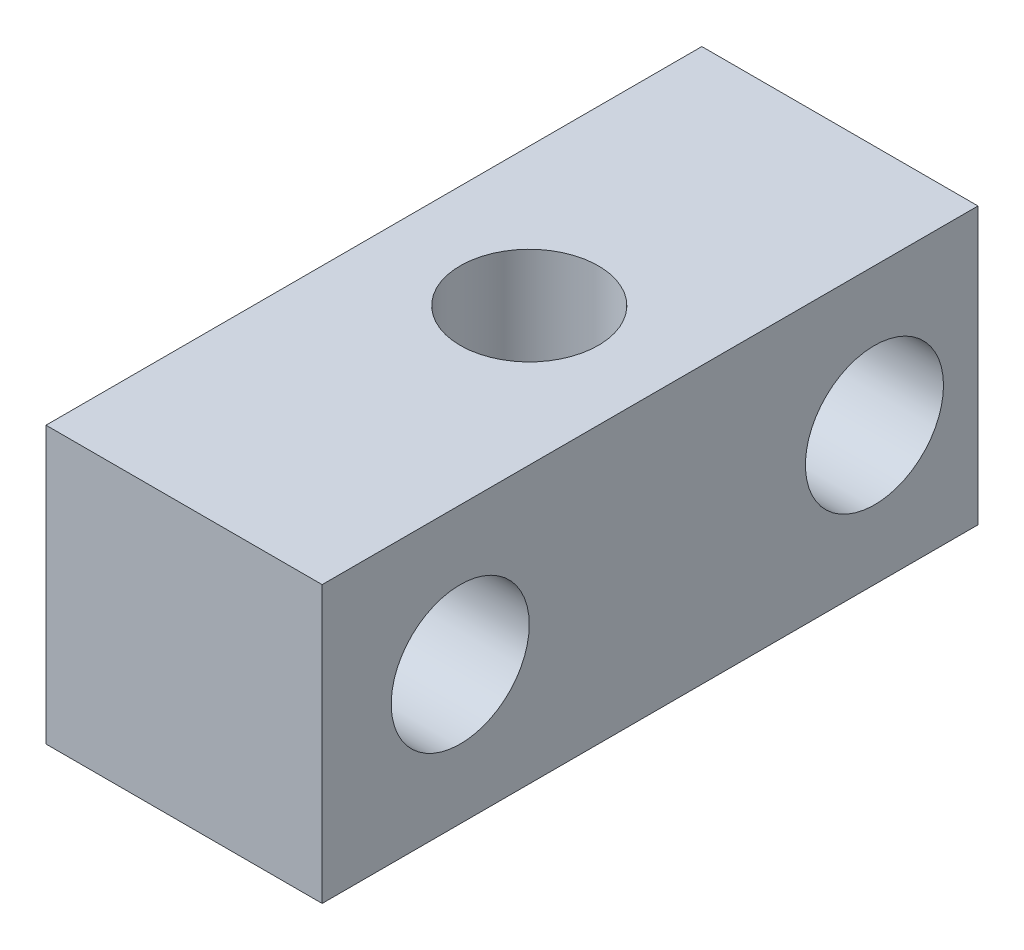
SolidWorks part; units mm, degrees
material "6061-T6 (SS)"
ref_plane "Front Plane" through (0, 0, 0) normal (0, 0, 1) x (1, 0, 0)
ref_plane "Top Plane" through (0, 0, 0) normal (0, 1, 0) x (1, 0, 0)
ref_plane "Right Plane" through (0, 0, 0) normal (1, 0, 0) x (0, 0, -1)
sketch "Sketch1" plane through (0, 0, 0) normal (0, 0, 1) x (1, 0, 0)
  line L1 (-6.35, -6.35) -> (6.35, -6.35)
  line L2 (-6.35, -6.35) -> (-6.35, 6.35)
  line L3 (-6.35, 6.35) -> (6.35, 6.35)
  line L4 (6.35, -6.35) -> (6.35, 6.35)
extrude "Boss-Extrude1" add sketch "Sketch1" along normal mid plane 69.85
hole_wizard "1/4-20 Tapped Hole1" positions "Sketch3" profile "Sketch2" tap size "1/4-20" standard "ANSI Inch" end condition through all
sketch "Sketch3" plane through (0, 6.35, 0) normal (0, 1, 0) x (1, 0, 0)
  point P0 (0, 0)
  point P3 (0, 19.05)
  point P5 (0, -19.05)
sketch "Sketch2" plane through (0, 6.35, 0) normal (1, 0, 0) x (0, 0, 1)
  line L0 (0, 0) -> (0, 12.7)
  line L1 (0, 12.7) -> (3.175, 12.7)
  line L2 (3.175, 12.7) -> (3.175, 0)
  line L5 (3.175, 0) -> (0, 0)
  line L11 (0, -6.35) -> (0, 107.95) construction
  dimension "Thread Major Dia." = 6.35
  dimension "Thru Tap Drill Depth" = 12.7
hole_wizard "1/4-20 Tapped Hole2" positions "Sketch5" profile "Sketch4" tap size "1/4-20" standard "ANSI Inch" end condition through all
sketch "Sketch5" plane through (6.35, 0, 0) normal (1, 0, 0) x (0, 0, -1)
  point P0 (9.525, 0)
  point P2 (28.575, 0)
  point P4 (-9.525, 0)
  point P6 (-28.575, 0)
  dimension "D1" = 19.05
  dimension "D2" = 19.05
  dimension "D3" = 19.05
sketch "Sketch4" plane through (6.35, 0, -9.525) normal (0, 1, 0) x (0, 0, -1)
  line L0 (0, 0) -> (0, 12.7)
  line L1 (0, 12.7) -> (3.175, 12.7)
  line L2 (3.175, 12.7) -> (3.175, 0)
  line L5 (3.175, 0) -> (0, 0)
  line L11 (0, -6.35) -> (0, 107.95) construction
  dimension "Thread Major Dia." = 6.35
  dimension "Thru Tap Drill Depth" = 12.7
sketch "Sketch6" plane through (0, 6.35, 0) normal (0, 1, 0) x (1, 0, 0)
  line L0 (6.35, -34.925) -> (6.35, 34.925) construction
  line L3 (-6.35, -4.7625) -> (6.35, -4.7625)
  line L6 (-6.35, -4.7625) -> (6.35, -4.7625)
  line L7 (-6.35, -4.7625) -> (-6.35, 34.925)
  line L8 (-6.35, 34.925) -> (6.35, 34.925)
  line L9 (6.35, -4.7625) -> (6.35, 34.925)
  circle A1 centre (0, 0) radius 3.175 construction
  circle M5 centre (0, 0) radius 3.175
  line M6 (6.35, 34.925) -> (-6.35, 34.925)
  line M7 (-6.35, 34.925) -> (-6.35, -34.925)
  line M9 (6.35, -34.925) -> (6.35, 34.925)
  circle M11 centre (0, 19.05) radius 3.175
  dimension "D1" = 4.7625
extrude "Cut-Extrude1" cut sketch "Sketch6" against normal through all contours L3 M7 M9 M6 M5 M11
